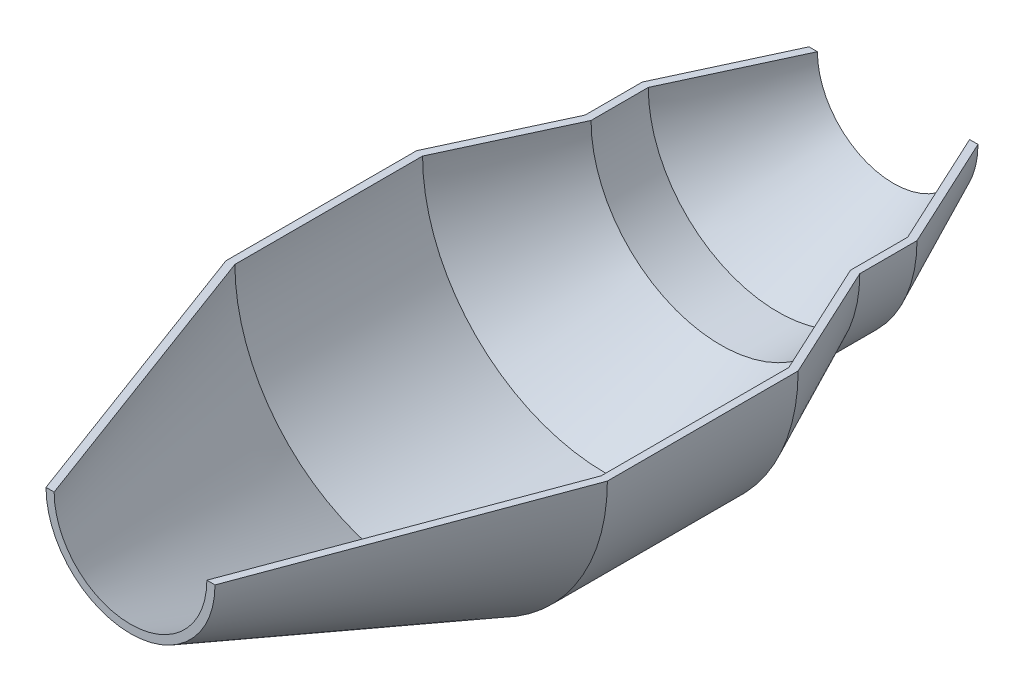
SolidWorks part; units mm, degrees
ref_plane "Front Plane" through (0, 0, 0) normal (0, 0, 1) x (1, 0, 0)
ref_plane "Top Plane" through (0, 0, 0) normal (0, 1, 0) x (1, 0, 0)
ref_plane "Right Plane" through (0, 0, 0) normal (1, 0, 0) x (0, 0, -1)
sketch "Sketch3" plane through (0, 0, 0) normal (1, 0, 0) x (0, 0, -1)
  line L0 (-100, 0) -> (100, 0) construction
  line L1 (-100, 0) -> (-100, -22.15) construction
  line L2 (-100, -22.15) -> (-25, -50)
  line L3 (-25, -50) -> (25, -50)
  line L4 (25, -50) -> (55.1616, -36)
  line L5 (100, -22.15) -> (100, 0) construction
  line L6 (0, 0) -> (0, -50) construction
  line L7 (100, 0) -> (-100, 0) construction
  line L8 (55.1616, -36) -> (70.1616, -36)
  line L9 (70.1616, -36) -> (100, -22.15)
  line L10 (-100, -20.0166) -> (-24.6407, -48)
  line L11 (-24.6407, -48) -> (24.5585, -48)
  line L12 (24.5585, -48) -> (54.72, -34)
  line L13 (54.72, -34) -> (69.72, -34)
  line L14 (69.72, -34) -> (100, -19.9451)
  line L15 (69.72, -34) -> (99.158, -20.3359) construction
  line L16 (-99.3038, -20.2751) -> (-24.6407, -48) construction
  line L17 (-100, -20.0166) -> (-100, -22.15)
  line L18 (100, -19.9451) -> (100, -22.15)
  point P4 (0, 0)
  dimension "D1" = 200
  dimension "D2" = 50
  dimension "D3" = 50
  dimension "D4" = 22.15
  dimension "D5" = 159.628
  dimension "D6" = 15
  dimension "D7" = 34
  dimension "D8" = 36
  dimension "D9" = 2
revolve "Revolve1" add sketch "Sketch3" angle 180 mid plane about L0
